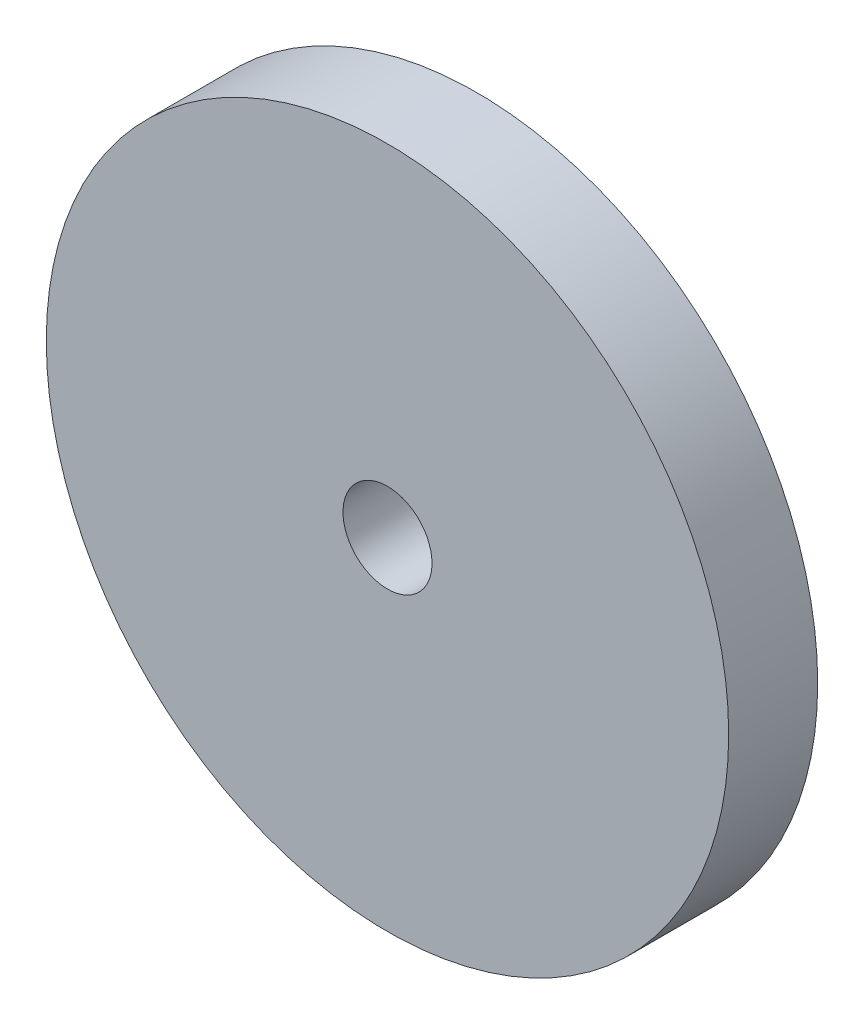
SolidWorks part; units mm, degrees
ref_plane "Alzado" through (0, 0, 0) normal (0, 0, 1) x (1, 0, 0)
ref_plane "Planta" through (0, 0, 0) normal (0, 1, 0) x (1, 0, 0)
ref_plane "Vista lateral" through (0, 0, 0) normal (1, 0, 0) x (0, 0, -1)
sketch "Croquis1" plane through (0, 0, 0) normal (0, 0, 1) x (1, 0, 0)
  circle A0 centre (0, 0) radius 11.5
  circle A1 centre (0, 0) radius 1.5
extrude "Saliente-Extruir1" add sketch "Croquis1" along normal blind 3 contours A1 | A0
